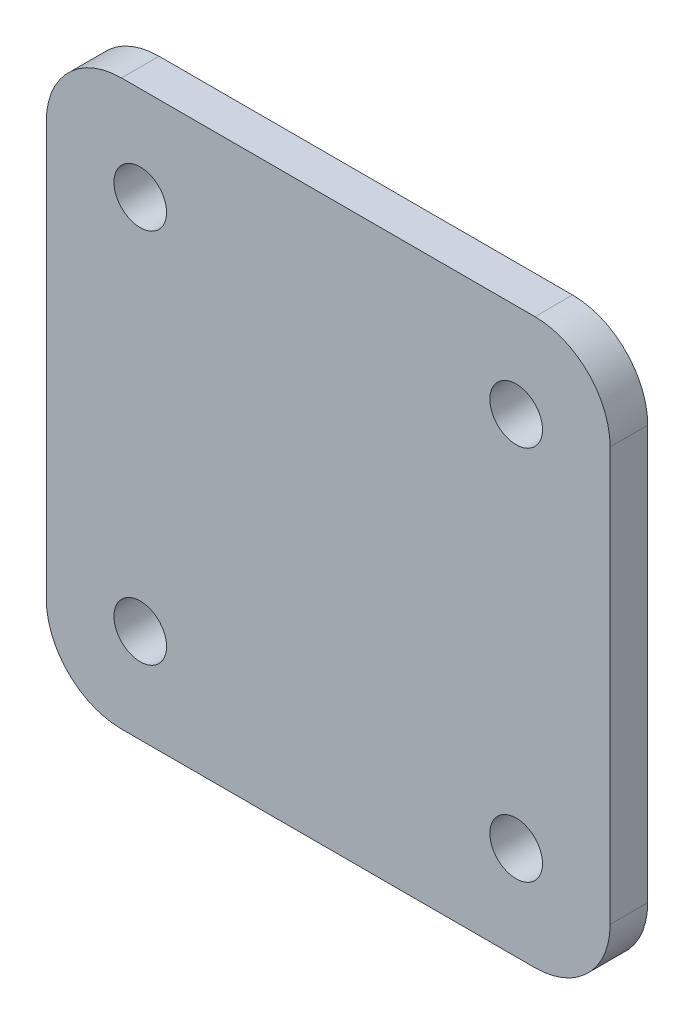
SolidWorks part; units mm, degrees
material "1.0545 (S355N)"
ref_plane "Front Plane" through (0, 0, 0) normal (0, 0, 1) x (1, 0, 0)
ref_plane "Top Plane" through (0, 0, 0) normal (0, 1, 0) x (1, 0, 0)
ref_plane "Right Plane" through (0, 0, 0) normal (1, 0, 0) x (0, 0, -1)
sketch "Sketch1" plane through (0, 0, 0) normal (0, 0, 1) x (1, 0, 0)
  line L0 (-36.5658, 0) -> (63.1228, 0) construction
  line L1 (0, 43.3719) -> (0, -42.4377) construction
  line L2 (-37.5, 37.5) -> (37.5, 37.5)
  line L3 (-37.5, 37.5) -> (-37.5, -37.5)
  line L4 (-37.5, -37.5) -> (37.5, -37.5)
  line L5 (37.5, 37.5) -> (37.5, -37.5)
  dimension "D1" = 75
extrude "Boss-Extrude1" add sketch "Sketch1" along normal blind 5
sketch "Sketch2" plane through (0, 0, 5) normal (0, 0, 1) x (1, 0, 0)
  line L0 (0, 39.5963) -> (0, -41.4866) construction
  line L1 (-42.2825, 0) -> (50.8385, 0) construction
  point P5 (-25, 25)
  point P6 (25, 25)
  point P7 (25, -25)
  point P8 (-25, -25)
  dimension "D1" = 50
  dimension "D2" = 50
hole_wizard "Ø7.0 (7) Diameter Hole1" positions "Sketch3" profile "Sketch4" hole size "Ø7.0" standard "ISO" end condition through all
sketch "Sketch3" plane through (0, 0, 5) normal (0, 0, 1) x (1, 0, 0)
  point P0 (-25, 25)
  point P3 (-25, -25)
  point P6 (25, -25)
  point P9 (25, 25)
sketch "Sketch4" plane through (-25, 25, 5) normal (1, 0, 0) x (0, -1, 0)
  line L0 (0, 0) -> (0, 5)
  line L1 (0, 5) -> (3.5, 5)
  line L2 (3.5, 5) -> (3.5, 0)
  line L5 (3.5, 0) -> (0, 0)
  line L11 (0, -6.35) -> (0, 107.95) construction
  dimension "Thru Hole Dia." = 7
  dimension "Thru Hole Depth" = 5
fillet "Fillet1" radius 10 4 edges at (-37.5, 37.5, 2.5) (-37.5, -37.5, 2.5) (37.5, -37.5, 2.5) (37.5, 37.5, 2.5)
